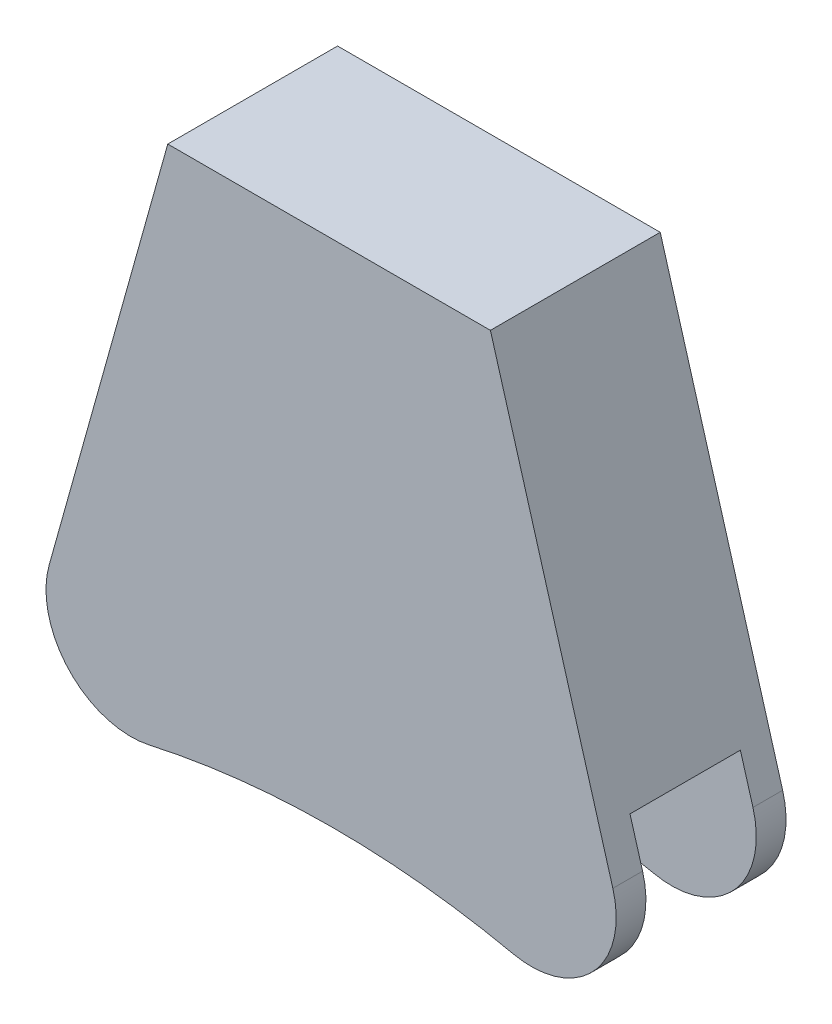
SolidWorks part; units mm, degrees
ref_plane "Front Plane" through (0, 0, 0) normal (0, 0, 1) x (1, 0, 0)
ref_plane "Top Plane" through (0, 0, 0) normal (0, 1, 0) x (1, 0, 0)
ref_plane "Right Plane" through (0, 0, 0) normal (1, 0, 0) x (0, 0, -1)
sketch "Sketch1" plane through (0, 0, 0) normal (0, 0, 1) x (1, 0, 0)
  line L0 (-1.4077, 0) -> (0, 0) construction
  line L2 (-1.4077, 0) -> (-1.4077, -160) construction
  line L3 (17.0486, 0) -> (36.6389, -67.5205)
  line L5 (36.6389, -67.5205) -> (-1.4077, -160) construction
  line L6 (-1.4077, -160) -> (-39.8975, -67.7041) construction
  line L7 (-39.8975, -67.7041) -> (-20.9514, 0)
  line L9 (-20.9514, 0) -> (17.0486, 0)
  circle A0 centre (-1.4077, -160) radius 100 construction
  arc A1 (-39.8975, -67.7041) -> (36.6389, -67.5205) centre (-1.4077, -160) cw
  point P0 (-1.4077, 0)
  point P9 (0, 0)
  dimension "D4" = 200
  dimension "D2" = 160
  dimension "D3" = 45
  dimension "D5" = 38
extrude "Boss-Extrude1" add sketch "Sketch1" along normal mid plane 20 contours L3 A1 L7 L9
sketch "Sketch4" plane through (0, 0, 0) normal (0, 0, 1) x (1, 0, 0)
  line L1 (11, 0) -> (-11, 0) construction
  circle A0 centre (-1.9514, -140) radius 100
  arc A2 (36.6389, -67.5205) -> (-39.8975, -67.7041) centre (-1.4077, -160) ccw construction
  point P2 (-1.957, 0)
  point P6 (0, 0)
  point P16 (-1.9514, 0)
  dimension "D1" = 200
  dimension "D2" = 20
  dimension "D3" = 19
  dimension "D4" = 0
sketch "Sketch5" plane through (0, 0, 0) normal (1, 0, 0) x (0, 0, -1)
  line L0 (0, -40) -> (0, -240) construction
  line L8 (0, -140) -> (87.2439, -140) construction
  line L13 (-6.5, -140) -> (6.5, -140)
  line L18 (-6.5, -140) -> (-6.5, -240)
  line L19 (-6.5, -240) -> (6.5, -240)
  line L20 (6.5, -140) -> (6.5, -240)
  line L21 (-6.5, -140) -> (6.5, -240) construction
  line L22 (-6.5, -240) -> (6.5, -140) construction
  point P0 (0, -190)
  point P7 (0, -223.9124)
  point P8 (0, -246)
  dimension "D1" = 13
  dimension "D2" = 100
  dimension "D3" = 50
revolve "Cut-Revolve2" cut sketch "Sketch5" angle 360 about L8
fillet "Fillet1" radius 10 4 edges at (36.6389, -67.5205, 8.25) (36.6389, -67.5205, -8.25) (-39.8975, -67.7041, -8.25) (-39.8975, -67.7041, 8.25)
